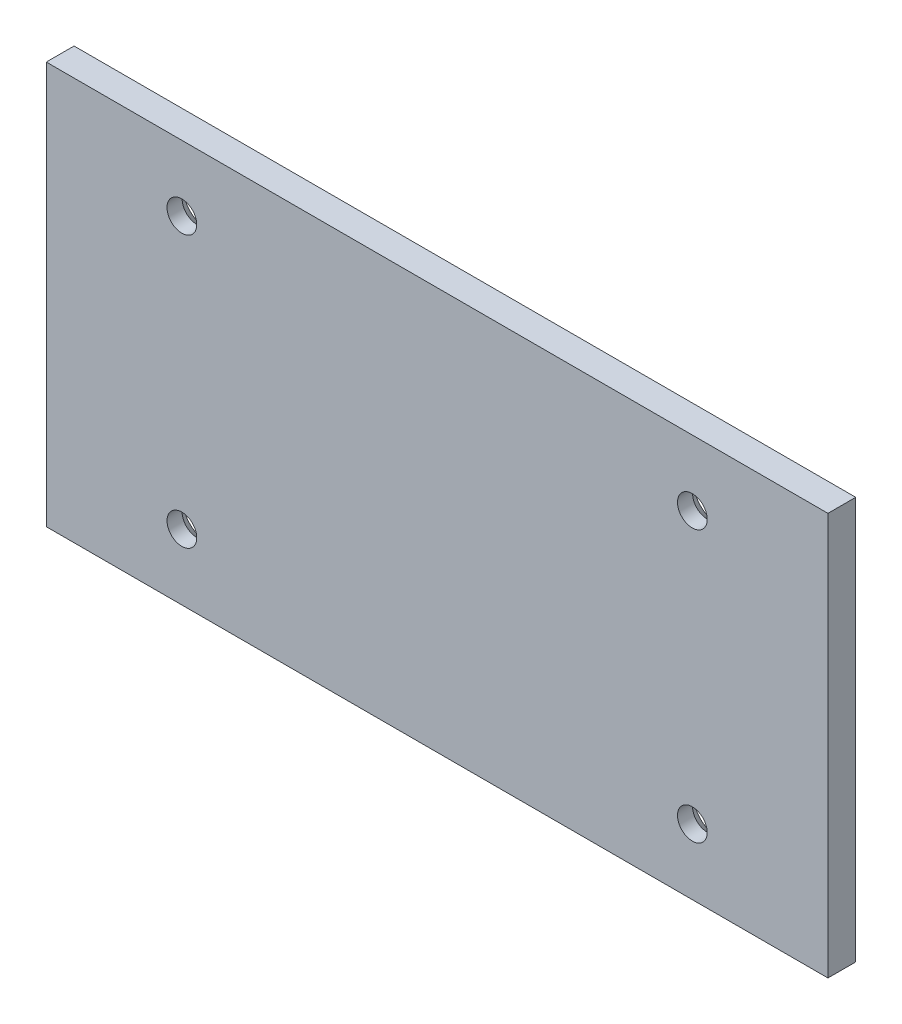
SolidWorks part; units mm, degrees
ref_plane "Top Plane" through (0, 0, 0) normal (0, 0, 1) x (1, 0, 0)
ref_plane "Front Plane" through (0, 0, 0) normal (0, 1, 0) x (1, 0, 0)
ref_plane "Right Plane" through (0, 0, 0) normal (1, 0, 0) x (0, 0, -1)
sketch "Profile Sketch" plane through (0, 0, 0) normal (0, 0, 1) x (1, 0, 0)
  line L0 (44.6745, 23) -> (44.6745, -23)
  line L1 (-44.6745, -23) -> (44.6745, -23)
  line L2 (-44.6745, -23) -> (-44.6745, 23)
  line L3 (-44.6745, 23) -> (44.6745, 23)
  line L5 (-44.6745, -23) -> (44.6745, 23) construction
  line L6 (-44.6745, 23) -> (44.6745, -23) construction
  point P0 (0, 0)
  point P6 (37.1745, 0)
  dimension "D1" = 89.3491
  dimension "D2" = 46
extrude "Profile Extrude" add sketch "Profile Sketch" along normal blind 3.175
sketch "Column Mounting Hole Sketch" plane through (0, 0, 0) normal (0, 0, 1) x (1, 0, 0)
  line L0 (0, 23) -> (0, -23) construction
  line L2 (-44.6745, 23) -> (-44.6745, -23) construction
  line L3 (-44.6745, 0) -> (44.6745, 0) construction
  line L4 (44.6745, -23) -> (44.6745, 23) construction
  line L5 (44.6745, 23) -> (-44.6745, 23) construction
  line L6 (-44.6745, -23) -> (44.6745, -23) construction
  line L7 (-44.6745, 23) -> (-44.6745, -23) construction
  point P6 (29.1755, 15.5)
  point P7 (-29.1755, 15.5)
  point P8 (-29.1755, -15.5)
  point P9 (29.1755, -15.5)
  dimension "D1" = 15.4991
  dimension "D2" = 7.5
hole_wizard "CSK for M3 Flat Head Machine Screw1" positions "3DSketch1" profile "Sketch1" countersink size "M3" standard "ANSI Metric" end condition through all
sketch3d "3DSketch1"
  point P0 (-29.1755, 15.5, 0)
  point P3 (-29.1755, -15.5, 0)
  point P6 (29.1755, -15.5, 0)
  point P9 (29.1755, 15.5, 0)
sketch "Sketch1" plane through (-29.1755, 15.5, 0) normal (1, 0, 0) x (0, 1, 0)
  line L0 (0, 0) -> (0, 3.175)
  line L1 (0, 3.175) -> (1.7, 3.175)
  line L2 (1.7, 3.175) -> (1.7, 1.45)
  line L3 (1.7, 1.45) -> (3.15, 0)
  line L5 (3.15, 0) -> (0, 0)
  line L6 (-1.7, 1.45) -> (-3.15, 0) construction
  line L11 (0, -6.35) -> (0, 107.95) construction
  dimension "Thru Hole Dia." = 3.4
  dimension "Thru Hole Depth" = 3.175
  dimension "Near C'Sink Dia." = 6.3
  dimension "Near C'Sink Angle" = 90
